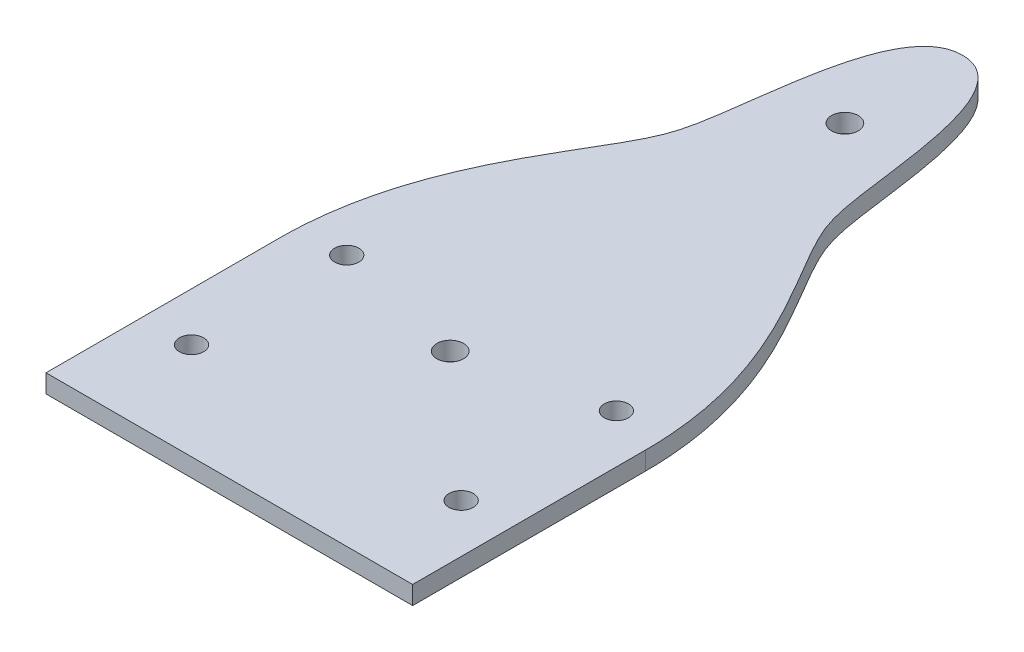
SolidWorks part; units mm, degrees
material "PC High Viscosity"
ref_plane "Front Plane" through (0, 0, 0) normal (0, 0, 1) x (1, 0, 0)
ref_plane "Top Plane" through (0, 0, 0) normal (0, 1, 0) x (1, 0, 0)
ref_plane "Right Plane" through (0, 0, 0) normal (1, 0, 0) x (0, 0, -1)
sketch "Sketch1" plane through (0, 0, 0) normal (0, 1, 0) x (1, 0, 0)
  line L1 (-30, -60) -> (30, -60)
  line L2 (-30, -60) -> (-30, 60)
  line L3 (-30, 60) -> (30, 60)
  line L4 (30, -60) -> (30, 60)
  line L5 (-30, -60) -> (30, 60) construction
  line L6 (-30, 60) -> (30, -60) construction
  point P0 (0, 0)
  dimension "D1" = 60
  dimension "D2" = 120
extrude "Boss-Extrude1" add sketch "Sketch1" along normal blind 3
sketch "Sketch2" plane through (0, 3, 0) normal (0, 1, 0) x (1, 0, 0)
  line L0 (0, -60) -> (0, 60) construction
  line L1 (-30, -60) -> (30, -60) construction
  line L2 (30, 60) -> (-30, 60) construction
  circle A1 centre (0, -23.856) radius 2.185
  circle A2 centre (0, 40.736) radius 2.185
  dimension "D2" = 4.37
  dimension "D3" = 64.592
  dimension "D1" = 36.144
extrude "Cut-Extrude1" cut sketch "Sketch2" against normal through all
sketch "Sketch3" plane through (0, 3, 0) normal (0, 1, 0) x (1, 0, 0)
  line L0 (0, 60) -> (0, -60) construction
  line L1 (30, 60) -> (-30, 60) construction
  line L2 (-30, -60) -> (30, -60) construction
  line L3 (30, -60) -> (30, 60) construction
  line L4 (30, -21.9) -> (30, 60)
  line L5 (30, 60) -> (0, 60)
  spline S0 degree 3 poles (0, 60) (9.9069, 60) (10.1167, 32.514) (16.2164, 16.2533) (30, -0.6861) (30, -21.9) knots 0 0 0 0 0.419463 0.519463 1 1 1 1
  dimension "D1" = 38.1
extrude "Cut-Extrude2" cut sketch "Sketch3" against normal through all
mirror "Mirror1" about plane through (0, 0, 0) normal (1, 0, 0) of "Cut-Extrude2"
sketch "Sketch4" plane through (0, 3, 0) normal (0, 1, 0) x (1, 0, 0)
  line L0 (-30, -60) -> (30, -60) construction
  line L1 (30, -60) -> (30, -21.9) construction
  line L2 (0, -60) -> (0, 60) construction
  circle A0 centre (22.0625, -44.125) radius 1.9844
  circle A1 centre (22.0625, -18.725) radius 1.9844
  circle A2 centre (-22.0625, -18.725) radius 1.9844
  circle A3 centre (-22.0625, -44.125) radius 1.9844
  dimension "D1" = 3.9688
  dimension "D2" = 25.4
  dimension "D3" = 15.875
  dimension "D4" = 7.9375
extrude "Cut-Extrude3" cut sketch "Sketch4" against normal through all
equation "\"pulley_pitch_diam\"= 12.73mm"
equation "\"pulley_total_width\"= 16mm"
equation "\"pulley_total_diam\"= 16mm"
equation "\"belt_width\"= 6mm"
equation "\"material_thickness\"= 3mm"
equation "\"shaft_diam\"= 8mm"
equation "\"bearing_od\"= 22mm"
equation "\"bearing_thickness\"= 7mm"
equation "\"D1@Boss-Extrude1\"=\"material_thickness\""
